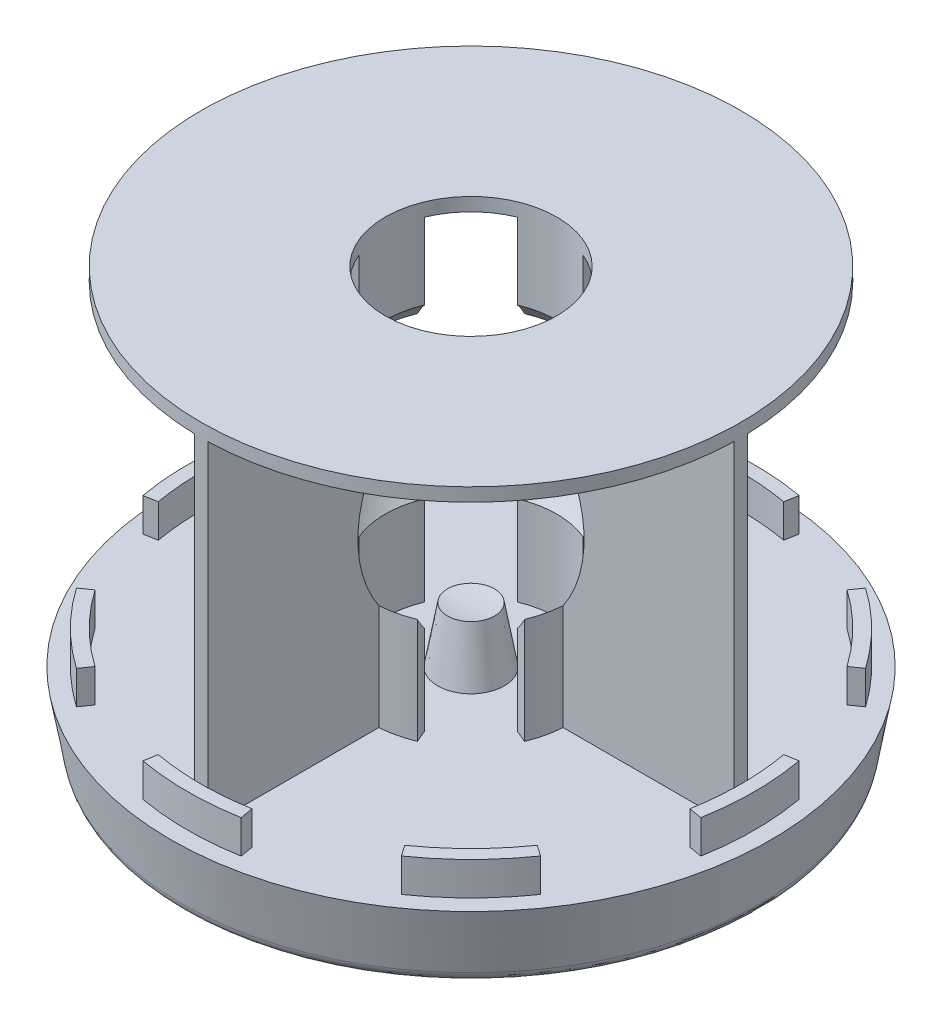
SolidWorks part; units mm, degrees
ref_plane "Front Plane" through (0, 0, 0) normal (0, 0, 1) x (1, 0, 0)
ref_plane "Top Plane" through (0, 0, 0) normal (0, 1, 0) x (1, 0, 0)
ref_plane "Right Plane" through (0, 0, 0) normal (1, 0, 0) x (0, 0, -1)
sketch "Sketch1" plane through (0, 0, 0) normal (0, 1, 0) x (1, 0, 0)
  circle A0 centre (0, 0) radius 2250
  dimension "D1" = 4500
extrude "Boss-Extrude1" add sketch "Sketch1" against normal blind 500 draft 10
sketch "Sketch2" plane through (0, -500, 0) normal (0, -1, 0) x (1, 0, 0)
  circle A0 centre (0, 0) radius 2161.8365
extrude "Boss-Extrude2" add sketch "Sketch2" along normal blind 500 draft 60
fillet "Fillet1" radius 100 1 edges at (0, -500, -2161.8365)
sketch "Sketch3" plane through (0, 0, 0) normal (0, 1, 0) x (1, 0, 0)
  line L0 (0, 0) -> (0, 2125)
  line L1 (0, 0) -> (390.7084, 2215.8174)
  line L2 (0, 0) -> (-390.7084, 2215.8174)
  circle A0 centre (0, 0) radius 2250
  circle A1 centre (0, 0) radius 2125
  circle A2 centre (0, 0) radius 2025
  dimension "D1" = 4250
  dimension "D4" = 4050
  dimension "D2" = 10
  dimension "D3" = 10
extrude "Boss-Extrude3" add sketch "Sketch3" along normal blind 250 contours A2 L1 A1 L0 | A2 L0 A1 L2
pattern_circular "CirPattern1" count 8 over 360 about axis through (0, 0, 0) along (0, 1, 0) of "Boss-Extrude3"
sketch "Sketch5" plane through (0, 0, 0) normal (0, 1, 0) x (1, 0, 0)
  line L5 (50, 743.0608) -> (50, 2025)
  line L10 (-50, 743.0608) -> (-50, 2025)
  line L11 (-50, 2025) -> (50, 2025)
  line L13 (246.0887, 594.1107) -> (284.357, 686.4986)
  line L14 (50, 741.3766) -> (50, 743.0608)
  line L17 (-50, 741.3766) -> (-50, 743.0608)
  line L19 (-246.0887, 594.1107) -> (-284.357, 686.4986)
  circle A0 centre (0, 0) radius 643.0608
  arc A1 (-50, 741.3766) -> (50, 741.3766) centre (0, 0) ccw
  circle A3 centre (0, 0) radius 743.0608 construction
  arc M31 (351.6376, 1994.2357) -> (-351.6376, 1994.2357) centre (0, 0) ccw
  dimension "D1" = 100
extrude "Boss-Extrude5" add sketch "Sketch5" along normal blind 2500 contours L13 A1 L14 L5 L10 L17 L19 A0 M31
pattern_circular "CirPattern2" count 4 over 360 about axis through (0, 0, 0) along (0, 1, 0) of "Boss-Extrude5"
sketch "Sketch6" plane through (0, 2500, 0) normal (0, 1, 0) x (1, 0, 0)
  circle A0 centre (0, 0) radius 643.0608
  circle A1 centre (0, 0) radius 2025
extrude "Boss-Extrude6" add sketch "Sketch6" along normal blind 100
sketch "Sketch9" plane through (0, 0, 0) normal (0, 1, 0) x (1, 0, 0)
  circle A0 centre (0, 0) radius 250
  dimension "D1" = 500
extrude "Boss-Extrude7" add sketch "Sketch9" along normal blind 500 draft 10
sketch "Sketch7" plane through (0, 0, 0) normal (0, 0, 1) x (1, 0, 0)
  line L0 (0, -1000) -> (0, 2600) construction
  line L1 (-1295.8111, -1000) -> (1295.8111, -1000) construction
  line L2 (2025, 2600) -> (-2025, 2600) construction
  line L3 (0, 0) -> (0, 2600)
  arc A0 (0, 400) -> (0, 2200) centre (0, 1300) ccw
  dimension "D1" = 1800
revolve "Cut-Revolve2" cut sketch "Sketch7" angle 360 about L0
